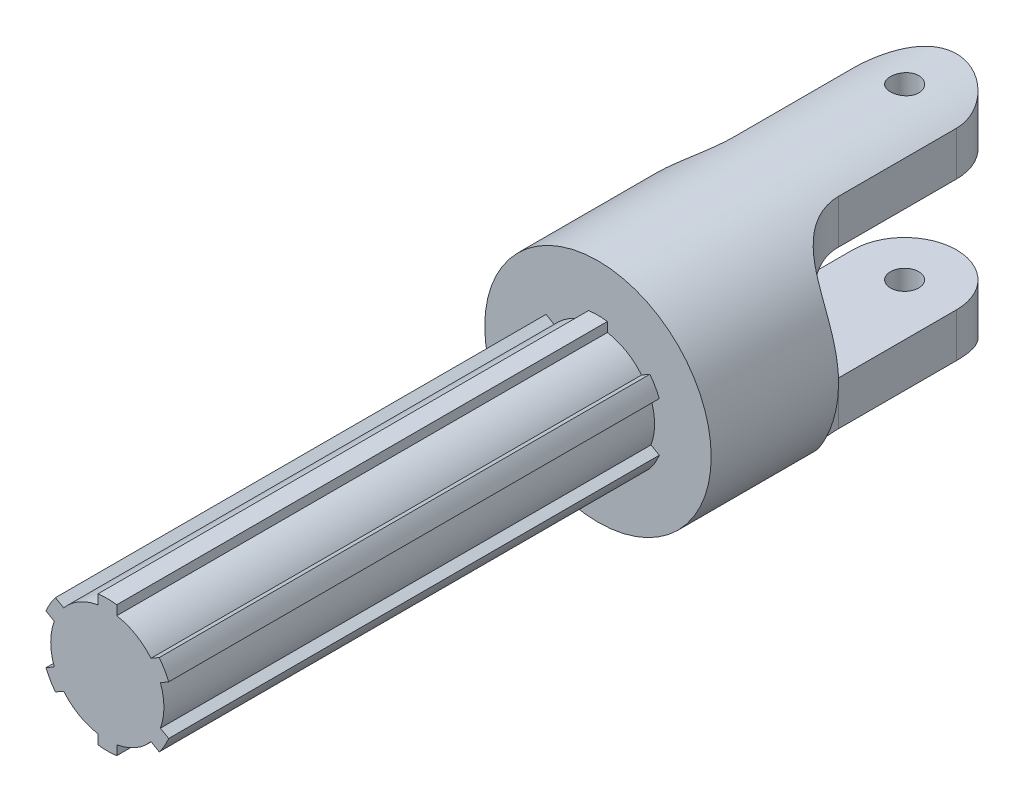
SolidWorks part; units mm, degrees
ref_plane "前视基准面" through (0, 0, 0) normal (0, 0, 1) x (1, 0, 0)
ref_plane "上视基准面" through (0, 0, 0) normal (0, 1, 0) x (1, 0, 0)
ref_plane "右视基准面" through (0, 0, 0) normal (1, 0, 0) x (0, 0, -1)
sketch "草图1" plane through (0, 0, 0) normal (0, 0, 1) x (1, 0, 0)
  circle A0 centre (0, 0) radius 6
  circle A1 centre (0, 0) radius 2.5
  dimension "D1" = 12
  dimension "D2" = 5
extrude "凸台-拉伸1" add sketch "草图1" along normal blind 19
sketch "草图2" plane through (0, 0, 0) normal (0, 1, 0) x (1, 0, 0)
  line L0 (0, 3.1848) -> (0, -21.7389) construction
  line L1 (-11.4446, -9) -> (14.3905, -9) construction
  line L2 (-2.75, -2.75) -> (-2.75, -9)
  line L4 (-6, 0) -> (-6, -19) construction
  line L5 (-6, -19) -> (6, -19) construction
  line L6 (-6, -2.0062) -> (-6, -15.979) construction
  line L7 (-6, -12.25) -> (-6, -19)
  line L8 (-6, -19) -> (6, -19)
  line L9 (6, -12.25) -> (6, -19)
  line L10 (2.75, -2.75) -> (2.75, -9)
  arc A0 (2.75, -2.75) -> (-2.75, -2.75) centre (0, -2.75) ccw
  arc A2 (-6, -12.25) -> (-2.75, -9) centre (-6, -9) ccw
  arc A3 (6, -12.25) -> (2.75, -9) centre (6, -9) cw
  circle A4 centre (0, -2.75) radius 0.75
  dimension "D1" = 5.5
  dimension "D2" = 10
  dimension "D3" = 1.5
extrude "切除-拉伸1" cut sketch "草图2" against normal mid plane 19 flip side to cut
sketch "草图3" plane through (0, 0, 0) normal (1, 0, 0) x (0, 0, -1)
  line L0 (-21.1395, 0) -> (4.4517, 0) construction
  line L1 (-9.25, 3) -> (0, 3)
  line L2 (0, 2.5) -> (0, 6) construction
  line L3 (0, 3) -> (0, -3)
  line L4 (0, -6) -> (0, -2.5) construction
  line L5 (0, -3) -> (-9.25, -3)
  arc A0 (-9.25, 3) -> (-9.25, -3) centre (-9.25, 0) ccw
  spline S1 degree 3 poles (-9, 5.3327) (-9.3489, 5.3327) (-9.6897, 5.3051) (-10.1779, 5.2159) (-10.3329, 5.1787) (-10.6283, 5.0872) (-10.7698, 5.0323) (-11.0313, 4.9047) (-11.1508, 4.8325) (-11.3691, 4.6696) (-11.4686, 4.5779) (-11.6436, 4.3792) (-11.7196, 4.2721) (-11.8523, 4.0422) (-11.9093, 3.9185) (-12.0526, 3.5326) (-12.1137, 3.2543) (-12.1762, 2.8069) (-12.192, 2.6524) (-12.2163, 2.34) (-12.2248, 2.1814) (-12.2435, 1.6983) (-12.2472, 1.3667) (-12.2504, 0.6843) (-12.25, 0.3412) (-12.25, -0.3433) (-12.2504, -0.687) (-12.2472, -1.3688) (-12.2435, -1.6999) (-12.2185, -2.3429) (-12.1972, -2.6566) (-12.1136, -3.2548) (-12.0524, -3.5333) (-11.9091, -3.9189) (-11.8521, -4.0427) (-11.7194, -4.2724) (-11.6436, -4.3792) (-11.4694, -4.577) (-11.3699, -4.6689) (-11.1511, -4.8323) (-11.032, -4.9042) (-10.7735, -5.0307) (-10.6328, -5.0857) (-10.3348, -5.1783) (-10.1798, -5.2154) (-9.8578, -5.2745) (-9.6895, -5.2965) (-9.3474, -5.3255) (-9.1746, -5.3327) (-9, -5.3327) knots 0 0 0 0 0.0625 0.0625 0.09375 0.09375 0.125 0.125 0.15625 0.15625 0.1875 0.1875 0.21875 0.21875 0.25 0.25 0.3125 0.3125 0.34375 0.34375 0.375 0.375 0.4375 0.4375 0.5 0.5 0.5625 0.5625 0.625 0.625 0.6875 0.6875 0.75 0.75 0.78125 0.78125 0.8125 0.8125 0.84375 0.84375 0.875 0.875 0.90625 0.90625 0.9375 0.9375 0.96875 0.96875 1 1 1 1 construction
  dimension "D1" = 6
extrude "切除-拉伸2" cut sketch "草图3" against normal mid plane 19
ref_plane "基准面1" through (0, 0, 14) normal (0, 0, -1) x (-1, 0, 0)
sketch "草图5" plane through (0, 0, 14) normal (0, 0, -1) x (-1, 0, 0)
  line L0 (-8.3423, 0) -> (11.464, 0) construction
  line L1 (0, 6.9225) -> (0, -7.7515) construction
  line L2 (-0.5, 3.4641) -> (-0.5, 2.958)
  line L3 (0.5, 3.4641) -> (0.5, 2.958)
  line L4 (2.75, 2.1651) -> (2.3117, 1.912)
  line L5 (3.25, 1.299) -> (2.8117, 1.046)
  line L6 (3.25, -1.299) -> (2.8117, -1.046)
  line L7 (2.75, -2.1651) -> (2.3117, -1.912)
  line L8 (0.5, -3.4641) -> (0.5, -2.958)
  line L9 (-0.5, -3.4641) -> (-0.5, -2.958)
  line L10 (-2.75, -2.1651) -> (-2.3117, -1.912)
  line L11 (-3.25, -1.299) -> (-2.8117, -1.046)
  line L12 (-3.25, 1.299) -> (-2.8117, 1.046)
  line L13 (-2.75, 2.1651) -> (-2.3117, 1.912)
  line L14 (0, 0) -> (0.5, 2.958) construction
  arc A0 (-0.5, 2.958) -> (-2.3117, 1.912) centre (0, 0) ccw
  arc A1 (0.5, 3.4641) -> (-0.5, 3.4641) centre (0, 0) ccw
  arc A2 (3.25, 1.299) -> (2.75, 2.1651) centre (0, 0) ccw
  arc A3 (2.75, -2.1651) -> (3.25, -1.299) centre (0, 0) ccw
  arc A4 (-0.5, -3.4641) -> (0.5, -3.4641) centre (0, 0) ccw
  arc A5 (-3.25, -1.299) -> (-2.75, -2.1651) centre (0, 0) ccw
  arc A6 (-2.75, 2.1651) -> (-3.25, 1.299) centre (0, 0) ccw
  arc A7 (2.3117, 1.912) -> (0.5, 2.958) centre (0, 0) ccw
  arc A8 (2.8117, -1.046) -> (2.8117, 1.046) centre (0, 0) ccw
  arc A9 (0.5, -2.958) -> (2.3117, -1.912) centre (0, 0) ccw
  arc A10 (-2.3117, -1.912) -> (-0.5, -2.958) centre (0, 0) ccw
  arc A11 (-2.8117, 1.046) -> (-2.8117, -1.046) centre (0, 0) ccw
  dimension "D1" = 6
  dimension "D2" = 7
  dimension "D3" = 1
extrude "凸台-拉伸2" add sketch "草图5" against normal blind 31
